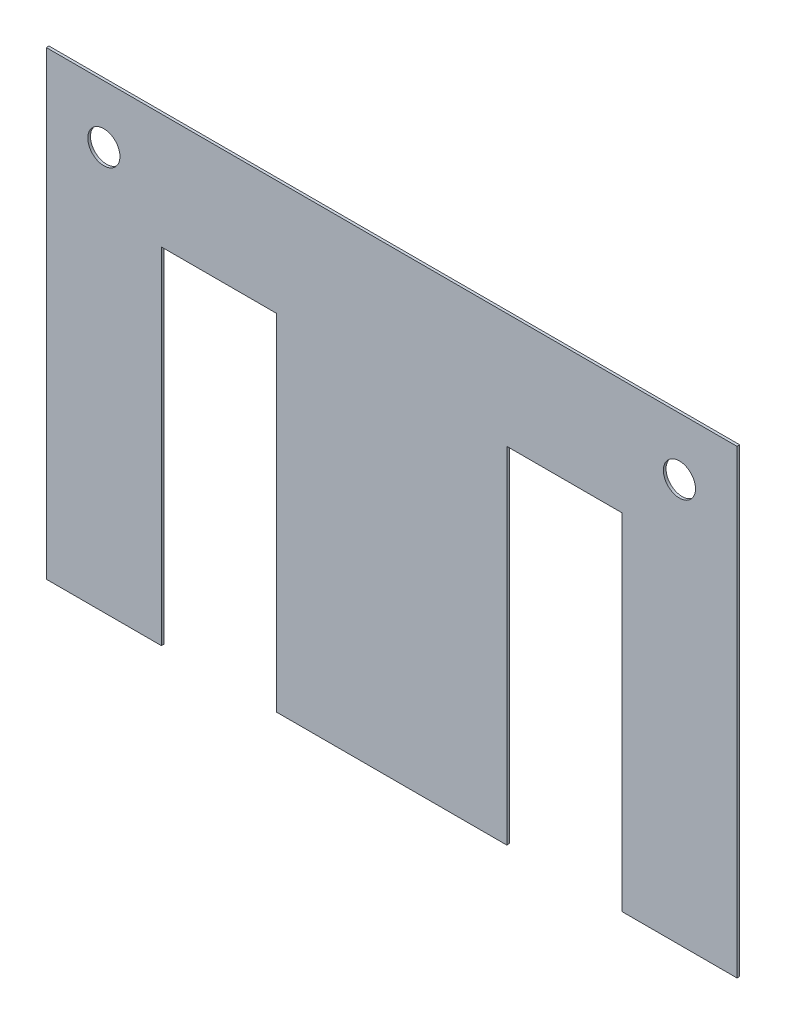
SolidWorks part; units mm, degrees
material "Chrome Stainless Steel"
ref_plane "Front Plane" through (0, 0, 0) normal (0, 0, 1) x (1, 0, 0)
ref_plane "Top Plane" through (0, 0, 0) normal (0, 1, 0) x (1, 0, 0)
ref_plane "Right Plane" through (0, 0, 0) normal (1, 0, 0) x (0, 0, -1)
sketch "Sketch1" plane through (0, 0, 0) normal (0, 0, 1) x (1, 0, 0)
  line L0 (0, 0) -> (0, 86)
  line L1 (0, 86) -> (129, 86)
  line L2 (129, 86) -> (129, 0)
  line L3 (129, 0) -> (107.5, 0)
  line L4 (107.5, 0) -> (107.5, 64.5)
  line L5 (107.5, 64.5) -> (86, 64.5)
  line L6 (86, 64.5) -> (86, 0)
  line L7 (86, 0) -> (43, 0)
  line L8 (43, 0) -> (43, 64.5)
  line L9 (43, 64.5) -> (21.5, 64.5)
  line L10 (21.5, 64.5) -> (21.5, 0)
  line L11 (21.5, 0) -> (0, 0)
  line L12 (64.5, 91.7114) -> (64.5, -9.9401) construction
  circle A0 centre (10.75, 75.25) radius 3
  circle A1 centre (118.25, 75.25) radius 3
  dimension "D7" = 6
  dimension "D1" = 129
  dimension "D2" = 86
  dimension "D3" = 21.5
  dimension "D4" = 21.5
  dimension "D5" = 43
  dimension "D6" = 64.5
  dimension "D9" = 107.5
  dimension "D10" = 10.75
extrude "Boss-Extrude1" add sketch "Sketch1" along normal blind 0.5
